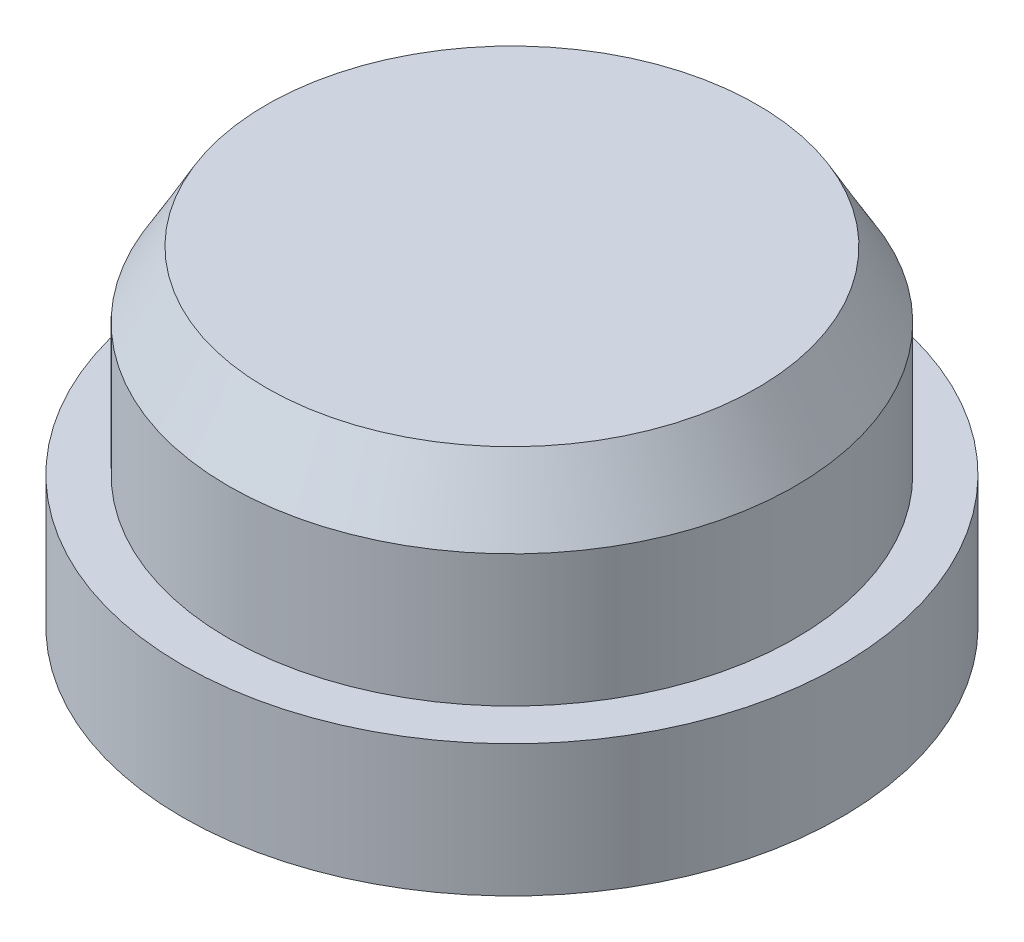
SolidWorks part; units mm, degrees
ref_plane "Спереди" through (0, 0, 0) normal (0, 0, 1) x (1, 0, 0)
ref_plane "Сверху" through (0, 0, 0) normal (0, 1, 0) x (1, 0, 0)
ref_plane "Справа" through (0, 0, 0) normal (1, 0, 0) x (0, 0, -1)
sketch "Sketch1" plane through (0, 0, 0) normal (0, 1, 0) x (1, 0, 0)
  circle A0 centre (0, 0) radius 5
  dimension "D1" = 10
extrude "Boss-Extrude1" add sketch "Sketch1" along normal blind 2
sketch "Sketch2" plane through (0, 2, 0) normal (0, 1, 0) x (1, 0, 0)
  circle A0 centre (0, 0) radius 4.3
  dimension "D1" = 8.6
extrude "Boss-Extrude2" add sketch "Sketch2" along normal blind 3
chamfer "Chamfer1" distance 1 angle 30 1 edges at (0, 5, 4.3)
